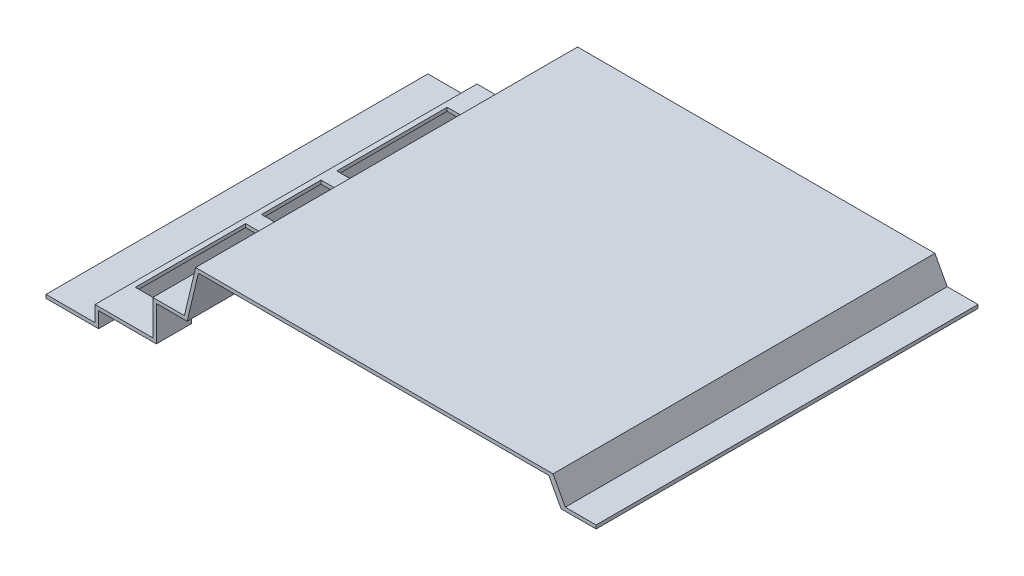
SolidWorks part; units mm, degrees
ref_plane "Płaszczyzna przednia" through (0, 0, 0) normal (0, 0, 1) x (1, 0, 0)
ref_plane "Płaszczyzna górna" through (0, 0, 0) normal (0, 1, 0) x (1, 0, 0)
ref_plane "Płaszczyzna prawa" through (0, 0, 0) normal (1, 0, 0) x (0, 0, -1)
sketch "Szkic1" plane through (0, 0, 0) normal (0, 0, 1) x (1, 0, 0)
  line L0 (0, 0) -> (0, 2)
  line L1 (0, 2) -> (28, 2)
  line L2 (28, 2) -> (28, 11)
  line L3 (28, 11) -> (61, 11)
  line L4 (61, 11) -> (61, 31)
  line L5 (61, 31) -> (79, 31)
  line L6 (79, 31) -> (85.4198, 58)
  line L7 (85.4198, 58) -> (289.4198, 58)
  line L8 (289.4198, 58) -> (296.4198, 45)
  line L9 (296.4198, 45) -> (314, 45)
  line L10 (314, 45) -> (314, 43)
  line L11 (314, 43) -> (294, 43)
  line L12 (294, 43) -> (287, 56)
  line L13 (287, 56) -> (87, 56)
  line L14 (87, 56) -> (80.5802, 29)
  line L15 (80.5802, 29) -> (63, 29)
  line L16 (63, 29) -> (63, 9)
  line L17 (63, 9) -> (30, 9)
  line L18 (30, 9) -> (30, 0)
  line L19 (30, 0) -> (0, 0)
  dimension "D1" = 20
  dimension "D2" = 7
  dimension "D3" = 200
  dimension "D4" = 204
  dimension "D5" = 2
  dimension "D6" = 2
  dimension "D7" = 2
  dimension "D8" = 2
  dimension "D9" = 2
  dimension "D10" = 2
  dimension "D11" = 2
  dimension "D12" = 2
  dimension "D13" = 28
  dimension "D14" = 314
  dimension "D15" = 9
  dimension "D16" = 20
  dimension "D17" = 18
  dimension "D18" = 33
  dimension "D19" = 58
  dimension "D20" = 15
  dimension "D21" = 17.5802
extrude "Dodanie-wyciągnięcie1" add sketch "Szkic1" along normal mid plane 218
sketch "Szkic2" plane through (0, 11, 0) normal (0, 1, 0) x (1, 0, 0)
  line L0 (61, -109) -> (61, 109) construction
  line L1 (61, 89) -> (31, 89)
  line L2 (61, 89) -> (61, 26)
  line L3 (61, 26) -> (31, 26)
  line L4 (31, 89) -> (31, 26)
  line L5 (61, 109) -> (28, 109) construction
  line L6 (61, 17) -> (31, 17)
  line L7 (61, 17) -> (61, -17)
  line L8 (61, -17) -> (31, -17)
  line L9 (31, 17) -> (31, -17)
  line L10 (61, -26) -> (31, -26)
  line L11 (61, -26) -> (61, -89)
  line L12 (61, -89) -> (31, -89)
  line L13 (31, -26) -> (31, -89)
  dimension "D1" = 34
  dimension "D2" = 63
  dimension "D3" = 9
  dimension "D4" = 9
  dimension "D5" = 30
  dimension "D6" = 20
extrude "Wytnij-wyciągnięcie1" cut sketch "Szkic2" against normal up to surface (2 mm away) up to face at (46.5, 9, 0)
sketch "Szkic3" plane through (0, 31, 0) normal (0, 1, 0) x (1, 0, 0)
  line L0 (61, -109) -> (61, 109) construction
  line L1 (79, 109) -> (61, 109) construction
  point P0 (70, 0)
  dimension "D1" = 9
  dimension "D2" = 109
hole_wizard "Otwór pod śrubę M41" positions "Szkic 3D1" profile "Szkic4" hole size "M4" standard "ISO" end condition up to next
sketch3d "Szkic 3D1"
  point P0 (70, 31, 0)
sketch "Szkic4" plane through (70, 31, 0) normal (1, 0, 0) x (0, 0, 1)
  line L0 (0, 0) -> (0, 2)
  line L1 (0, 2) -> (2.25, 2)
  line L2 (2.25, 2) -> (2.25, 0)
  line L5 (2.25, 0) -> (0, 0)
  line L11 (0, -6.35) -> (0, 107.95) construction
  dimension "Średnica otworu na wylot" = 4.5
  dimension "Głębokość otworu na wylot" = 2
sketch "Szkic5" plane through (61, 0, 0) normal (-1, 0, 0) x (0, 0, 1)
  line L1 (-89, 9) -> (-61, 9)
  line L2 (-89, 9) -> (-89, 29)
  line L3 (-89, 29) -> (-61, 29)
  line L4 (-61, 9) -> (-61, 29)
  line L5 (89, 9) -> (61, 9)
  line L6 (89, 9) -> (89, 29)
  line L7 (89, 29) -> (61, 29)
  line L8 (61, 9) -> (61, 29)
  dimension "D1" = 28
  dimension "D2" = 28
  dimension "D3" = 20
  dimension "D4" = 20
extrude "Wytnij-wyciągnięcie2" cut sketch "Szkic5" against normal blind 3
